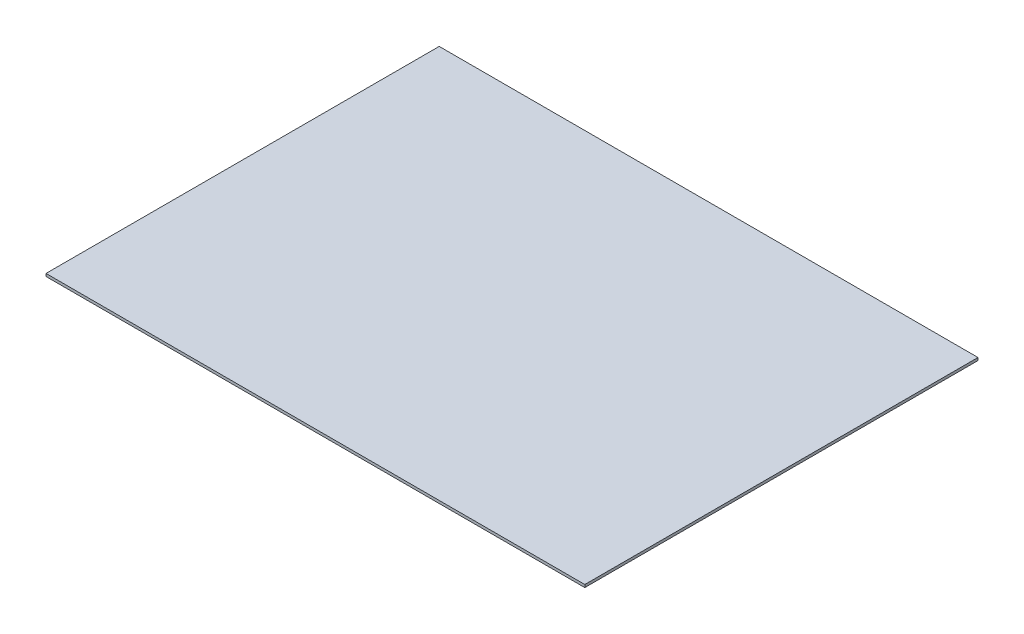
SolidWorks part; units mm, degrees
ref_plane "Front Plane" through (0, 0, 0) normal (0, 0, 1) x (1, 0, 0)
ref_plane "Top Plane" through (0, 0, 0) normal (0, 1, 0) x (1, 0, 0)
ref_plane "Right Plane" through (0, 0, 0) normal (1, 0, 0) x (0, 0, -1)
sketch "Sketch1" plane through (0, 0, 0) normal (0, 1, 0) x (1, 0, 0)
  line L1 (-200.8953, 146.6064) -> (200.8953, 146.6064)
  line L2 (-200.8953, 146.6064) -> (-200.8953, -146.6064)
  line L3 (-200.8953, -146.6064) -> (200.8953, -146.6064)
  line L4 (200.8953, 146.6064) -> (200.8953, -146.6064)
  line L5 (-200.8953, 146.6064) -> (200.8953, -146.6064) construction
  line L6 (-200.8953, -146.6064) -> (200.8953, 146.6064) construction
  point P0 (0, 0)
extrude "Boss-Extrude1" add sketch "Sketch1" along normal blind 2
